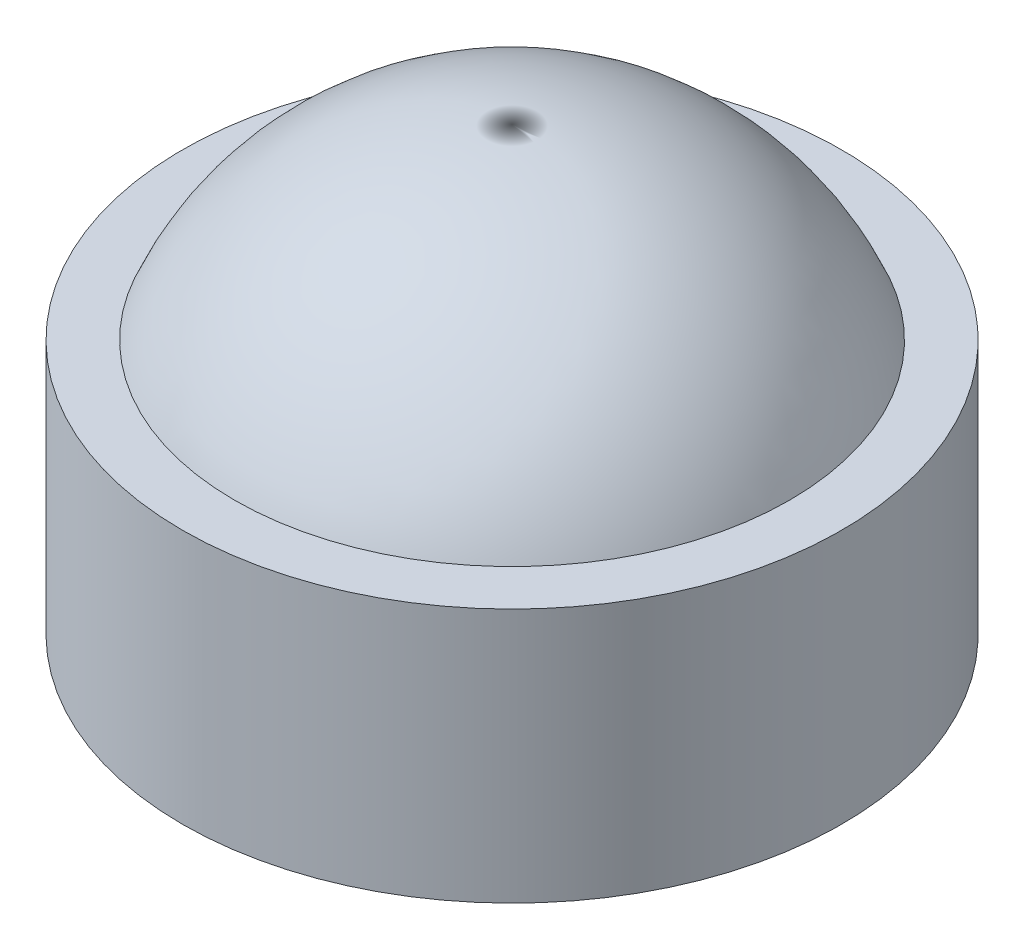
SolidWorks part; units mm, degrees
ref_plane "Front Plane" through (0, 0, 0) normal (0, 0, 1) x (1, 0, 0)
ref_plane "Top Plane" through (0, 0, 0) normal (0, 1, 0) x (1, 0, 0)
ref_plane "Right Plane" through (0, 0, 0) normal (1, 0, 0) x (0, 0, -1)
sketch "Sketch1" plane through (0, 0, 0) normal (0, 1, 0) x (1, 0, 0)
  circle A0 centre (0, 0) radius 0.011
  dimension "D1" = 0.022
extrude "Boss-Extrude1" add sketch "Sketch1" along normal blind 0.0085
ref_axis "Axis1" through (0, 0.0174, 0) along (0, -1, 0)
sketch "Sketch3" plane through (0, 0, 0) normal (0, 0, 1) x (1, 0, 0)
  line L6 (0, 0.0047) -> (0, 0.0147)
  line L7 (0, 0.0174) -> (0, -0.0066) construction
  line L8 (0, 0.0047) -> (-0.01, 0.0047)
  line L9 (-0.011, 0) -> (0.011, 0) construction
  arc A2 (-0.01, 0.0047) -> (0, 0.0147) centre (0, 0.0047) cw
  point P7 (0, 0)
  dimension "D1" = 0.01
  dimension "D2" = 0.0047
revolve "Revolve3" add sketch "Sketch3" angle 360 about axis through (0, 0.0174, 0) along (0, -1, 0)
